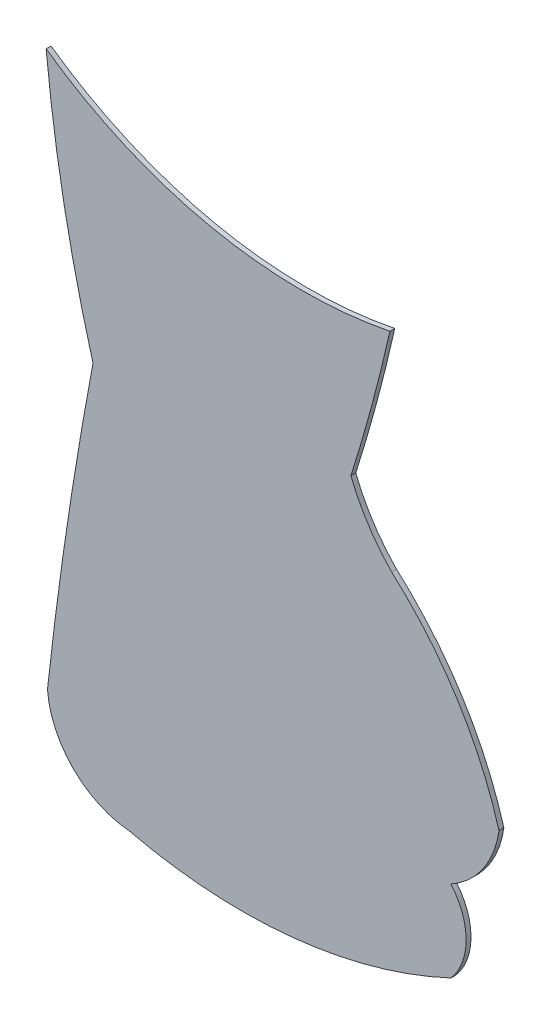
SolidWorks part; units mm, degrees
ref_plane "Alzado" through (0, 0, 0) normal (0, 0, 1) x (1, 0, 0)
ref_plane "Planta" through (0, 0, 0) normal (0, 1, 0) x (1, 0, 0)
ref_plane "Vista lateral" through (0, 0, 0) normal (1, 0, 0) x (0, 0, -1)
sketch "Model" plane through (0, 0, 0) normal (0, 0, 1) x (1, 0, 0)
  arc A0 (5.8203, 10.0054) -> (12.8593, 8.5163) centre (11.0755, 17.4657) ccw
  arc A1 (5.8203, 10.0054) -> (6.7797, 4.9098) centre (34.7357, 12.8118) ccw
  arc A2 (6.7797, 4.9098) -> (5.8469, -1.3445) centre (86.7306, -10.2116) ccw
  arc A3 (5.8469, -1.3445) -> (7.5145, -3.0117) centre (7.6658, -1.1927) ccw
  arc A4 (7.5145, -3.0117) -> (14.1082, -2.3286) centre (9.8326, 6.7776) ccw
  arc A5 (14.1082, -2.3286) -> (14.1079, -0.6612) centre (13.1512, -1.4951) ccw
  arc A6 (14.1079, -0.6612) -> (15.093, 0.7789) centre (13.1603, 1.0439) ccw
  arc A7 (15.093, 0.7789) -> (12.8946, 4.2649) centre (7.9395, -1.2961) ccw
  arc A8 (12.0607, 5.5532) -> (12.8946, 4.2649) centre (15.6984, 6.9938) ccw
  arc A9 (12.0607, 5.5532) -> (12.8593, 8.5163) centre (-21.7406, 16.2532) ccw
extrude "Saliente-Extruir1" add sketch "Model" along normal blind 0.1
